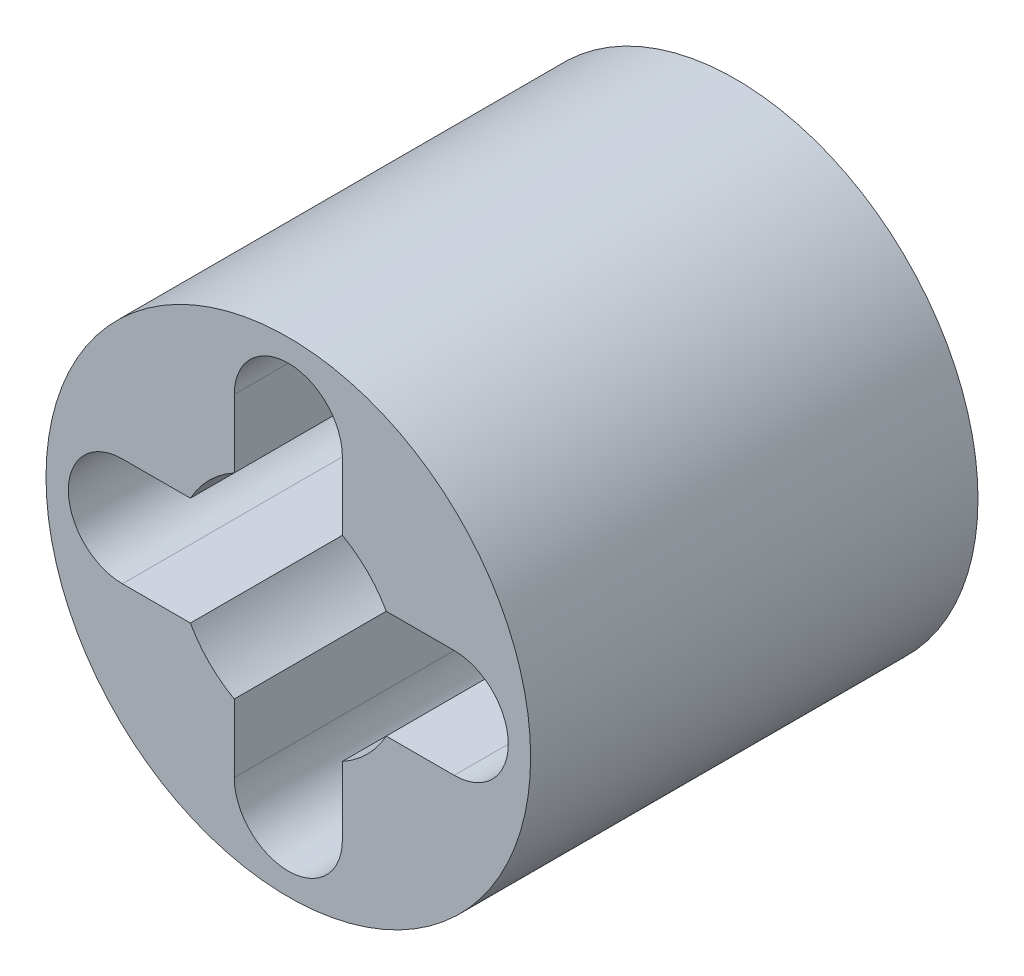
SolidWorks part; units mm, degrees
ref_plane "Plan de face" through (0, 0, 0) normal (0, 0, 1) x (1, 0, 0)
ref_plane "Plan de dessus" through (0, 0, 0) normal (0, 1, 0) x (1, 0, 0)
ref_plane "Plan de droite" through (0, 0, 0) normal (1, 0, 0) x (0, 0, -1)
sketch "Esquisse1" plane through (0, 0, 0) normal (0, 0, 1) x (1, 0, 0)
  line L0 (2.225, -0.725) -> (1.3132, -0.725)
  line L1 (2.225, 0.725) -> (1.3132, 0.725)
  line L2 (0.725, 2.225) -> (0.725, 1.3132)
  line L3 (-0.725, 2.225) -> (-0.725, 1.3132)
  line L4 (-2.225, 0.725) -> (-1.3132, 0.725)
  line L5 (-2.225, -0.725) -> (-1.3132, -0.725)
  line L6 (-0.725, -2.225) -> (-0.725, -1.3132)
  line L7 (0.725, -2.225) -> (0.725, -1.3132)
  circle A0 centre (0, 0) radius 3.25
  arc A1 (0.725, -1.3132) -> (1.3132, -0.725) centre (0, 0) ccw
  arc A2 (0.725, 2.225) -> (-0.725, 2.225) centre (0, 2.225) ccw
  arc A3 (2.225, -0.725) -> (2.225, 0.725) centre (2.225, 0) ccw
  arc A4 (-0.725, -2.225) -> (0.725, -2.225) centre (0, -2.225) ccw
  arc A5 (-2.225, 0.725) -> (-2.225, -0.725) centre (-2.225, 0) ccw
  arc A6 (-1.3132, -0.725) -> (-0.725, -1.3132) centre (0, 0) ccw
  arc A7 (-0.725, 1.3132) -> (-1.3132, 0.725) centre (0, 0) ccw
  arc A8 (1.3132, 0.725) -> (0.725, 1.3132) centre (0, 0) ccw
  point P14 (0, 0)
  dimension "D1" = 6.5
  dimension "D2" = 3
  dimension "D3" = 1.45
  dimension "D4" = 2.225
  dimension "D5" = 4
extrude "Boss.-Extru.1" add sketch "Esquisse1" along normal blind 6
